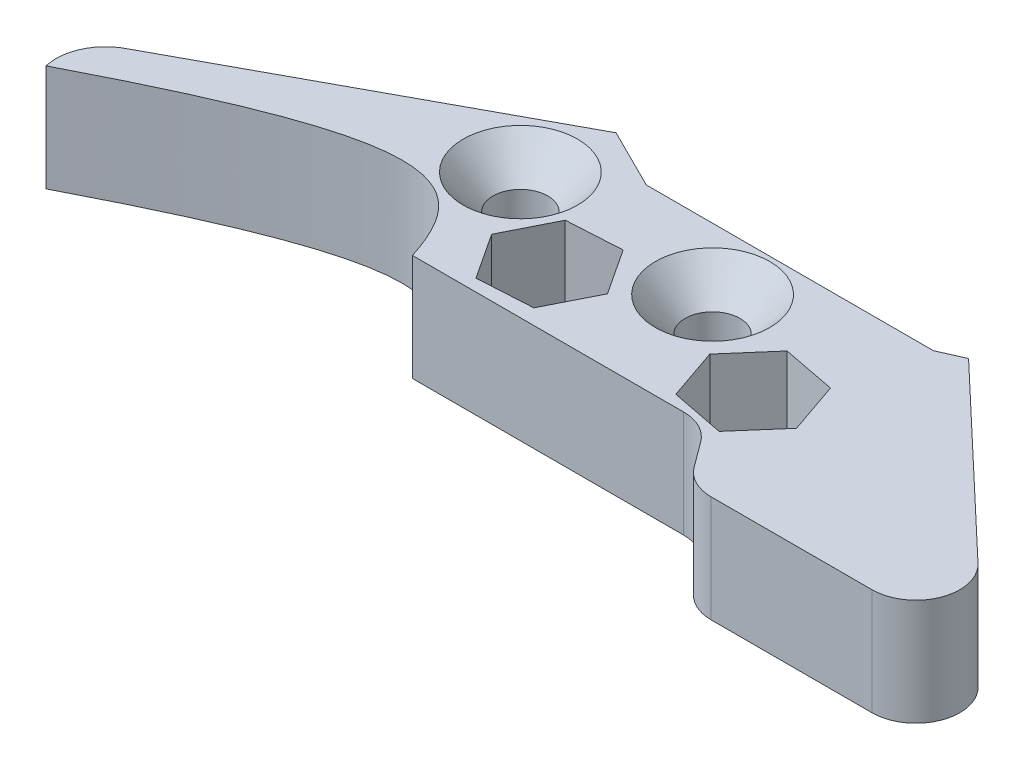
SolidWorks part; units mm, degrees
material "PE High Density"
ref_plane "Front Plane" through (0, 0, 0) normal (0, 0, 1) x (1, 0, 0)
ref_plane "Top Plane" through (0, 0, 0) normal (0, 1, 0) x (1, 0, 0)
ref_plane "Right Plane" through (0, 0, 0) normal (1, 0, 0) x (0, 0, -1)
sketch "Sketch1" plane through (0, 0, 0) normal (0, 1, 0) x (1, 0, 0)
  line L0 (98.733, -68.9858) -> (100.9426, -71.978)
  line L1 (62.3156, -66.9235) -> (94.6465, -66.9235)
  line L2 (61.7924, -42.1316) -> (24.0383, -62.5632)
  line L3 (61.7924, -42.1316) -> (68.9774, -45.7135)
  line L4 (68.9774, -45.7135) -> (103.1982, -45.7135)
  line L5 (103.1982, -45.7135) -> (106.0943, -44.4268)
  line L6 (106.0943, -44.4268) -> (127.8024, -65.01)
  line L7 (124.2019, -74.0403) -> (105.0291, -74.0403)
  arc A0 (94.6465, -66.9235) -> (98.733, -68.9858) centre (94.6465, -72.0035) cw
  arc A1 (24.0383, -62.5632) -> (22.2281, -71.7367) centre (26.6541, -67.8448) ccw construction
  arc A2 (24.0383, -62.5632) -> (26.6541, -73.7386) centre (26.6541, -67.8448) ccw construction
  circle A3 centre (60.1502, -51.8912) radius 3.2639
  arc A4 (24.0383, -62.5632) -> (20.9154, -69.188) centre (26.6541, -67.8448) ccw
  circle A5 centre (71.3764, -59.6418) radius 3.2639
  circle A6 centre (84.2377, -53.0771) radius 3.2639
  arc A7 (127.8024, -65.01) -> (124.2019, -74.0403) centre (124.2019, -68.8074) cw
  arc A8 (100.9426, -71.978) -> (105.0291, -74.0403) centre (105.0291, -68.9603) ccw
  arc A9 (124.2019, -74.0403) -> (127.8024, -65.01) centre (124.2019, -68.8074) ccw construction
  circle A10 centre (96.6303, -60.6336) radius 3.2639
  spline S0 degree 3 poles (62.3156, -66.9235) (58.5691, -55.0435) (51.4998, -53.4526) (20.9154, -69.188) knots 0 0 0 0 1 1 1 1
  point P0 (0, 0)
  dimension "D1" = 6.5278
extrude "Boss-Extrude1" add sketch "Sketch1" along normal blind 12.7
chamfer "Chamfer1" distance 4.0894 angle 41 2 edges at (84.2377, 12.7, 56.341) (60.1502, 12.7, 55.1551)
sketch "Sketch2" plane through (0, 12.7, 0) normal (0, 1, 0) x (1, 0, 0)
  line L1 (77.8986, -59.2634) -> (74.3097, -53.8043)
  line L2 (74.3097, -53.8043) -> (67.7876, -54.1827)
  line L3 (67.7876, -54.1827) -> (64.8543, -60.0203)
  line L4 (64.8543, -60.0203) -> (68.4431, -65.4794)
  line L5 (68.4431, -65.4794) -> (74.9653, -65.101)
  line L6 (74.9653, -65.101) -> (77.8986, -59.2634)
  line L7 (103.0428, -61.8834) -> (100.9189, -55.7052)
  line L8 (100.9189, -55.7052) -> (94.5064, -54.4554)
  line L9 (94.5064, -54.4554) -> (90.2178, -59.3838)
  line L10 (90.2178, -59.3838) -> (92.3417, -65.5621)
  line L11 (92.3417, -65.5621) -> (98.7542, -66.8119)
  line L12 (98.7542, -66.8119) -> (103.0428, -61.8834)
  circle A0 centre (71.3764, -59.6418) radius 5.6578 construction
  circle A1 centre (96.6303, -60.6336) radius 5.6578 construction
  dimension "D1" = 11.3157
extrude "Cut-Extrude1" cut sketch "Sketch2" against normal through all
